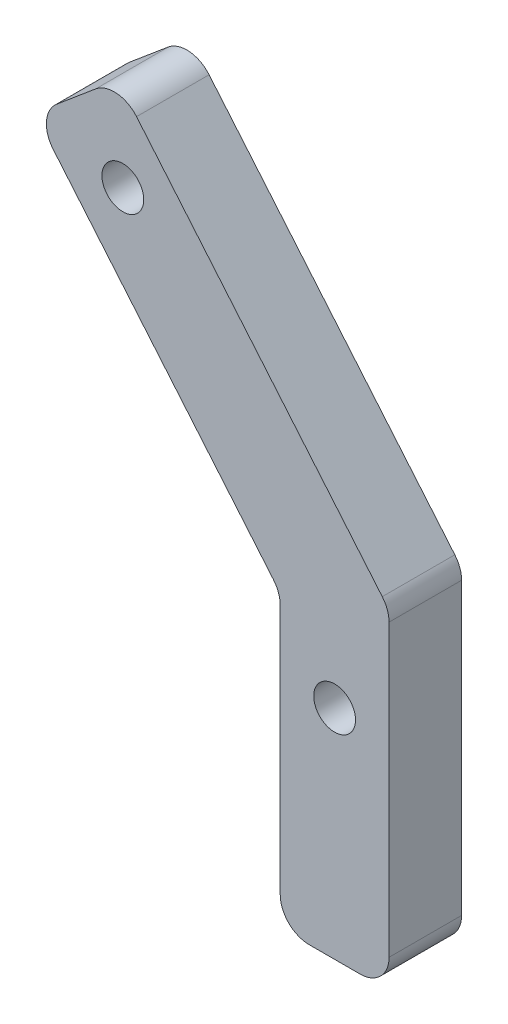
SolidWorks part; units mm, degrees
material "Acrylic (Medium-high impact)"
ref_plane "Front Plane" through (0, 0, 0) normal (0, 0, 1) x (1, 0, 0)
ref_plane "Top Plane" through (0, 0, 0) normal (0, 1, 0) x (1, 0, 0)
ref_plane "Right Plane" through (0, 0, 0) normal (1, 0, 0) x (0, 0, -1)
sketch "Sketch1" plane through (0, 0, 0) normal (0, 0, 1) x (1, 0, 0)
  line L0 (0, 0) -> (7.2966, 6.1226)
  line L1 (7.2966, 6.1226) -> (31.029, -22.1606)
  line L2 (31.029, -22.1606) -> (31.029, -51.0274)
  line L3 (0, 0) -> (21.504, -25.6274)
  line L4 (21.504, -25.6274) -> (21.504, -51.0274)
  line L5 (21.504, -51.0274) -> (31.029, -51.0274)
  dimension "D1" = 9.525
  dimension "D2" = 140
  dimension "D3" = 25.4
  dimension "D4" = 57.15
extrude "Boss-Extrude1" add sketch "Sketch1" along normal blind 6.35
fillet "Fillet1" radius 2.54 6 edges at (7.2966, 6.1226, 3.175) (0, 0, 3.175) (31.029, -51.0274, 3.175) (21.504, -51.0274, 3.175) (31.029, -22.1606, 3.175) (21.504, -25.6274, 3.175)
hole_wizard "#6 Clearance Hole1" positions "Sketch2" profile "Sketch3" hole size "#6" standard "ANSI Inch"
sketch "Sketch2" plane through (0, 0, 6.35) normal (0, 0, 1) x (1, 0, 0)
  line L0 (5.3508, 4.4899) -> (1.9458, 1.6327) construction
  line L1 (24.044, -51.0274) -> (28.489, -51.0274) construction
  line L2 (3.6483, 3.0613) -> (11.8117, -6.6675) construction
  line L4 (26.2665, -51.0274) -> (26.2665, -31.9774) construction
  line L6 (30.4347, -21.4524) -> (8.9293, 4.1768) construction
  point P0 (7.73, -1.8031)
  point P2 (26.2665, -31.9774)
  dimension "D1" = 6.35
  dimension "D2" = 19.05
sketch "Sketch3" plane through (7.73, -1.8031, 6.35) normal (1, 0, 0) x (0, -1, 0)
  line L0 (0, 0) -> (0, 11.2589)
  line L1 (0, 11.2589) -> (1.8288, 10.16)
  line L2 (1.8288, 10.16) -> (1.8288, 0)
  line L5 (1.8288, 0) -> (0, 0)
  line L10 (0, 11.2589) -> (-1.8288, 10.16) construction
  line L11 (0, -6.35) -> (0, 107.95) construction
  dimension "Hole Dia." = 3.6576
  dimension "Hole Depth" = 10.16
  dimension "Drill Angle" = 118
